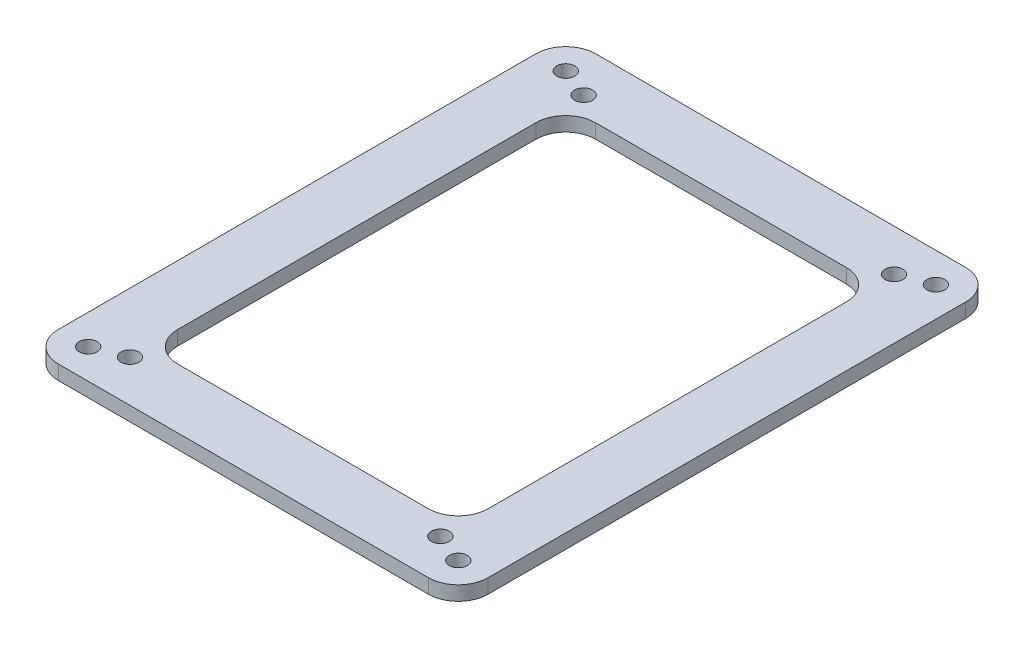
SolidWorks part; units mm, degrees
ref_plane "前基準面" through (0, 0, 0) normal (0, 0, 1) x (1, 0, 0)
ref_plane "上基準面" through (0, 0, 0) normal (0, 1, 0) x (1, 0, 0)
ref_plane "右基準面" through (0, 0, 0) normal (1, 0, 0) x (0, 0, -1)
sketch "草圖1" plane through (0, 0, 0) normal (0, 1, 0) x (1, 0, 0)
  line L0 (-48.3044, 0) -> (48.3044, 0) construction
  line L1 (0, -20.9833) -> (0, 20.9833) construction
  line L2 (-31, 45) -> (31, 45)
  line L3 (-31, -45) -> (31, -45)
  line L4 (-36, 40) -> (-36, -40)
  line L5 (-31, 30.7953) -> (-31, 49.2047) construction
  line L6 (-34.5828, 38) -> (-17.4172, 38) construction
  line L7 (-26, 35) -> (-26, -35)
  line L9 (-26, -35) -> (26, -35)
  line L10 (-26, 35) -> (26, 35)
  line L12 (36, 40) -> (36, -40)
  line L13 (26, 35) -> (26, -35)
  circle A0 centre (-26, 38) radius 1.5
  circle A1 centre (26, 38) radius 1.5
  circle A2 centre (26, -38) radius 1.5
  circle A3 centre (-26, -38) radius 1.5
  circle A4 centre (-31, 40) radius 1.5
  circle A5 centre (31, 40) radius 1.5
  circle A6 centre (-31, -40) radius 1.5
  circle A7 centre (31, -40) radius 1.5
  arc A8 (-36, 40) -> (-31, 45) centre (-31, 40) cw
  arc A11 (36, 40) -> (31, 45) centre (31, 40) ccw
  arc A12 (-36, -40) -> (-31, -45) centre (-31, -40) ccw
  arc A14 (36, -40) -> (31, -45) centre (31, -40) cw
  point P4 (0, 0)
  point P7 (0, 0)
  point P25 (-26, 40)
  point P26 (26, -29.7118)
  point P27 (57.3116, -28.0038)
  point P29 (26, -28.9798)
  point P30 (26, 26.4084)
  point P32 (-31, 40)
  point P35 (-26, 38)
  point P36 (-36, 0)
  point P37 (-26, 27.4684)
  point P46 (0, 28.9798)
  point P57 (-26, 0)
  point P58 (36, 0)
  point P60 (26, 0)
  dimension "D1" = 52
  dimension "D3" = 3
  dimension "D4" = 3
  dimension "D7" = 10
  dimension "D2" = 76
  dimension "D5" = 62
  dimension "D6" = 80
  dimension "D8" = 10
extrude "填料-伸長1" add sketch "草圖1" along normal blind 2.4
fillet "圓角1" radius 5 4 edges at (-26, 1.2, -35) (26, 1.2, -35) (26, 1.2, 35) (-26, 1.2, 35)
